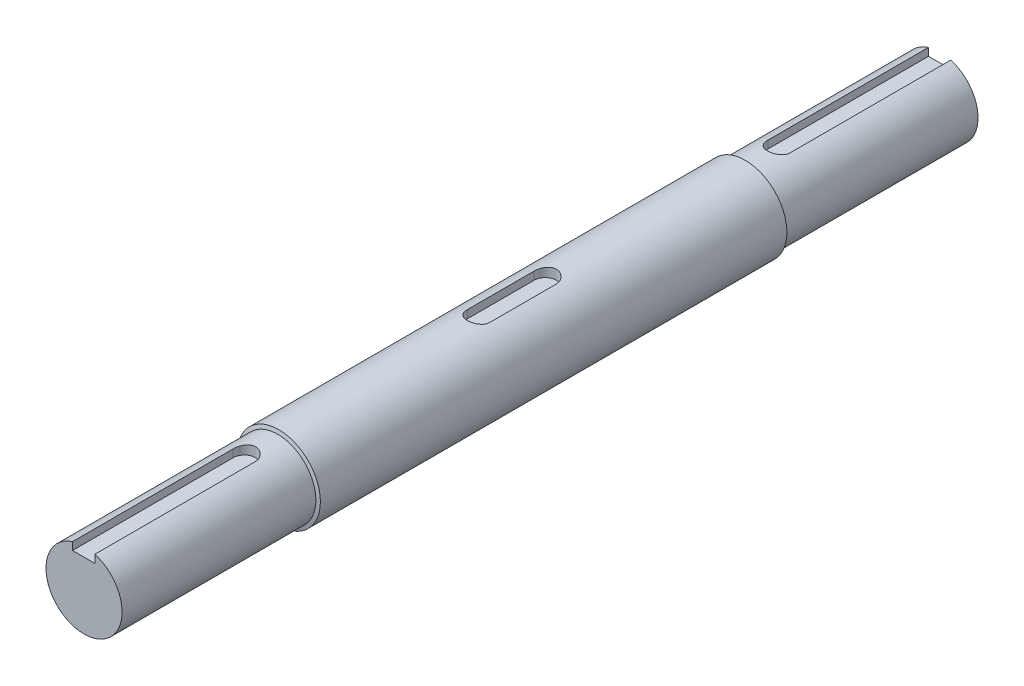
SolidWorks part; units mm, degrees
ref_plane "Front Plane" through (0, 0, 0) normal (0, 0, 1) x (1, 0, 0)
ref_plane "Top Plane" through (0, 0, 0) normal (0, 1, 0) x (1, 0, 0)
ref_plane "Right Plane" through (0, 0, 0) normal (1, 0, 0) x (0, 0, -1)
sketch "Sketch1" plane through (0, 0, 0) normal (0, 0, 1) x (1, 0, 0)
  circle A0 centre (0, 0) radius 8.75
  dimension "D1" = 17.5
extrude "Boss-Extrude1" add sketch "Sketch1" along normal blind 180
sketch "Sketch2" plane through (0, 0, 180) normal (0, 0, 1) x (1, 0, 0)
  circle A0 centre (0, 0) radius 8
  circle A1 centre (0, 0) radius 8.75 construction
  circle A2 centre (0, 0) radius 8.75
  dimension "D1" = 16
extrude "Cut-Extrude1" cut sketch "Sketch2" against normal blind 40.95
sketch "Sketch3" plane through (0, 0, 180) normal (0, 0, 1) x (1, 0, 0)
  line L0 (-2.423, 5.9996) -> (2.277, 5.9996)
  line L1 (2.277, 5.9996) -> (2.277, 7.6691)
  line L2 (-2.423, 5.9996) -> (-2.423, 7.6242)
  arc A3 (2.277, 7.6691) -> (-2.423, 7.6242) centre (0, 0) ccw
  point P3 (-0.073, 5.9996)
  dimension "D1" = 6
  dimension "D2" = 4.7
extrude "Cut-Extrude2" cut sketch "Sketch3" against normal blind 33.8
sketch "Sketch4" plane through (0, 5.9996, 0) normal (0, 1, 0) x (1, 0, 0)
  line L0 (-2.423, -146.2) -> (2.277, -146.2)
  arc A0 (-2.423, -146.2) -> (2.277, -146.2) centre (-0.073, -146.2) cw
extrude "Cut-Extrude3" cut sketch "Sketch4" along normal blind 33.8
ref_plane "Plane1" through (0, 0, 90) normal (0, 0, 1) x (1, 0, 0)
mirror "Mirror1" about plane through (0, 0, 90) normal (0, 0, 1) of "Cut-Extrude3", "Cut-Extrude1", "Cut-Extrude2"
ref_plane "Plane2" through (0, 6.75, 0) normal (0, 1, 0) x (1, 0, 0)
sketch "Sketch6" plane through (0, 6.75, 0) normal (0, 1, 0) x (1, 0, 0)
  line L3 (-2.35, -97) -> (-2.35, -83)
  line L4 (2.35, -97) -> (2.35, -83)
  arc A0 (2.35, -83) -> (-2.35, -83) centre (0, -83) ccw
  arc A1 (-2.35, -97) -> (2.35, -97) centre (0, -97) ccw
  dimension "D1" = 4.7
  dimension "D2" = 4.7
  dimension "D3" = 14
extrude "Cut-Extrude4" cut sketch "Sketch6" along normal blind 33.8
sketch "Sketch7" plane through (0, 0, 40.95) normal (0, 0, -1) x (-1, 0, 0)
  circle A1 centre (0, 0) radius 8.75
  circle A2 centre (0, 0) radius 8.75
  dimension "D1" = 0
extrude "Boss-Extrude2" add sketch "Sketch7" against normal blind 7.8
sketch "Sketch9" plane through (0, 0, 40.95) normal (0, 0, -1) x (-1, 0, 0)
  circle A1 centre (0, 0) radius 8.75
  circle A2 centre (0, 0) radius 8.75
  dimension "D1" = 0
extrude "Boss-Extrude3" add sketch "Sketch9" along normal blind 0.3 draft 75
mirror "Mirror4" about plane through (0, 0, 90) normal (0, 0, 1) of "Boss-Extrude3"
